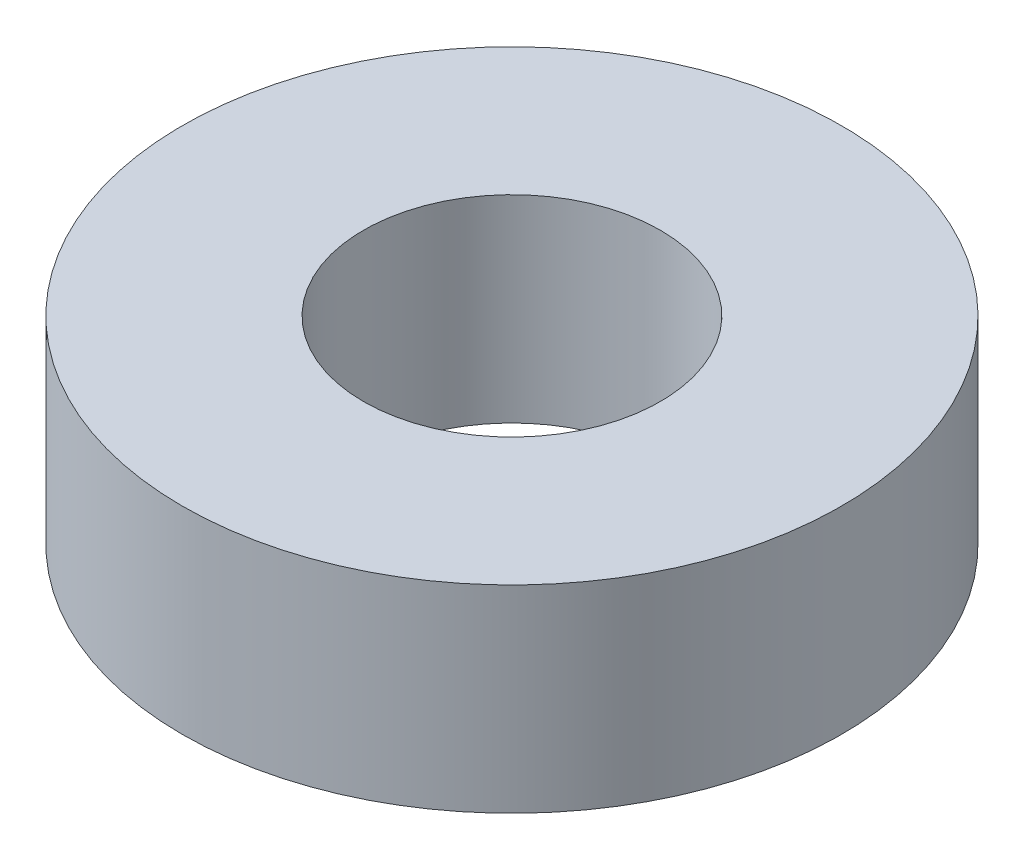
SolidWorks part; units mm, degrees
ref_plane "Front Plane" through (0, 0, 0) normal (0, 0, 1) x (1, 0, 0)
ref_plane "Top Plane" through (0, 0, 0) normal (0, 1, 0) x (1, 0, 0)
ref_plane "Right Plane" through (0, 0, 0) normal (1, 0, 0) x (0, 0, -1)
sketch "Sketch1" plane through (0, 0, 0) normal (0, 1, 0) x (1, 0, 0)
  circle A0 centre (0, 0) radius 7.5
  point P3 (0, 0)
  dimension "D1" = 15
extrude "Boss-Extrude1" add sketch "Sketch1" along normal blind 4.5
hole_wizard "1/4 Clearance Hole1" positions "Sketch2" profile "Sketch3" hole size "1/4" standard "ANSI Inch" end condition through all
sketch "Sketch2" plane through (0, 4.5, 0) normal (0, 1, 0) x (1, 0, 0)
  point P0 (0, 0)
sketch "Sketch3" plane through (0, 4.5, 0) normal (1, 0, 0) x (0, 0, 1)
  line L0 (0, 0) -> (0, 4.5)
  line L1 (0, 4.5) -> (3.3782, 4.5)
  line L2 (3.3782, 4.5) -> (3.3782, 0)
  line L5 (3.3782, 0) -> (0, 0)
  line L11 (0, -6.35) -> (0, 107.95) construction
  dimension "Thru Hole Dia." = 6.7564
  dimension "Thru Hole Depth" = 4.5
